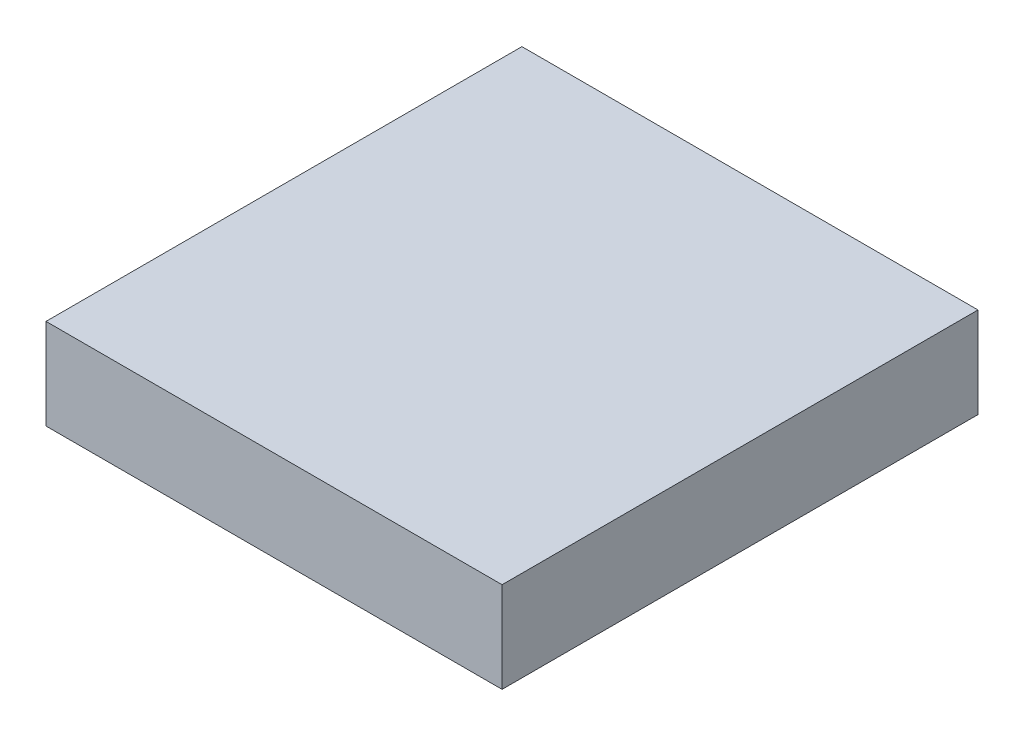
SolidWorks part; units mm, degrees
ref_plane "Спереди" through (0, 0, 0) normal (0, 0, 1) x (1, 0, 0)
ref_plane "Сверху" through (0, 0, 0) normal (0, 1, 0) x (1, 0, 0)
ref_plane "Справа" through (0, 0, 0) normal (1, 0, 0) x (0, 0, -1)
sketch "Эскиз1" plane through (0, 0, 0) normal (0, 1, 0) x (1, 0, 0)
  line L0 (-8.05, 8.4) -> (8.05, 8.4)
  line L1 (-8.05, 8.4) -> (-8.05, -8.4)
  line L2 (8.05, 8.4) -> (8.05, -8.4)
  line L3 (-8.05, -8.4) -> (8.05, -8.4)
  line L4 (-8.05, 8.4) -> (8.05, -8.4) construction
  line L5 (8.05, 8.4) -> (-8.05, -8.4) construction
  point P1 (0, 0)
extrude "Бобышка-Вытянуть1" add sketch "Эскиз1" along normal blind 3.2
